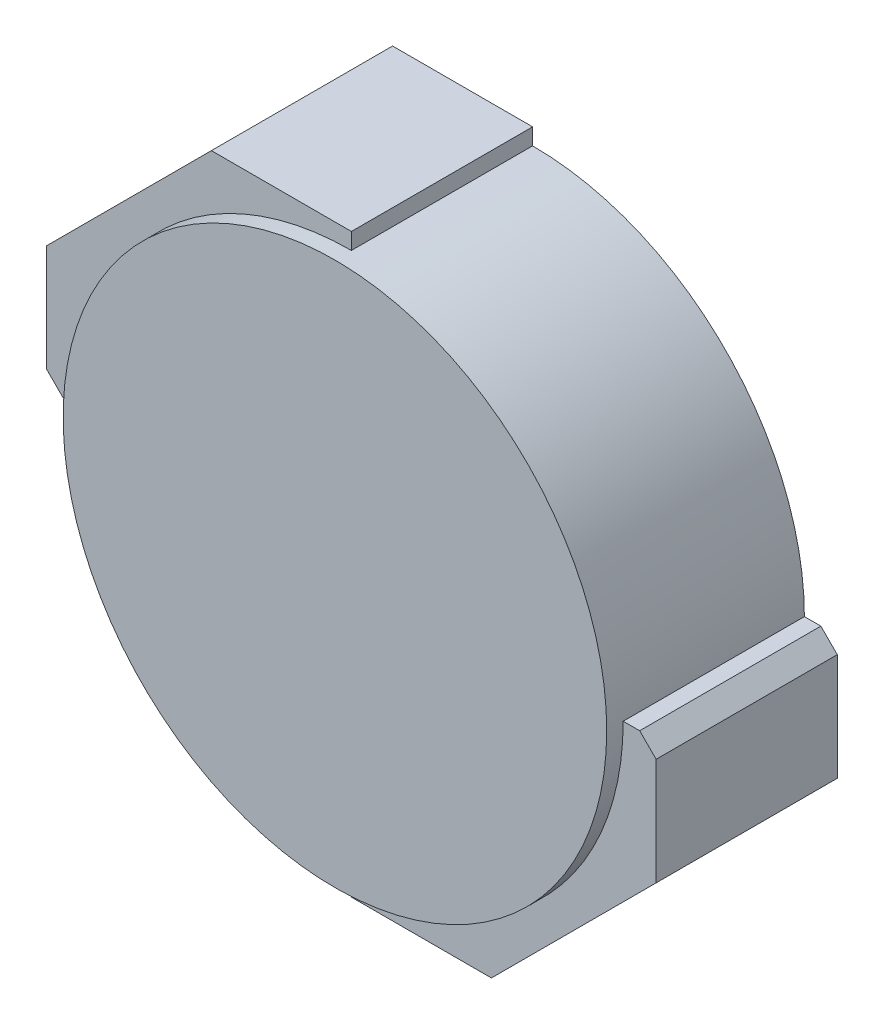
SolidWorks part; units mm, degrees
ref_plane "Front Plane" through (0, 0, 0) normal (0, 0, 1) x (1, 0, 0)
ref_plane "Top Plane" through (0, 0, 0) normal (0, 1, 0) x (1, 0, 0)
ref_plane "Right Plane" through (0, 0, 0) normal (1, 0, 0) x (0, 0, -1)
sketch "Sketch1" plane through (0, 0, 0) normal (0, 0, 1) x (1, 0, 0)
  circle A0 centre (0, 0) radius 1.65
extrude "Boss-Extrude1" add sketch "Sketch1" along normal blind 1.2
sketch "Sketch2" plane through (0, 0, 0) normal (0, 0, 1) x (1, 0, 0)
  line L5 (-1.85, 1.75) -> (0, 1.75)
  line L6 (-1.85, 1.75) -> (-1.85, 0)
  line L7 (-1.85, 0) -> (0, 0)
  line L8 (0, 1.75) -> (0, 0)
  line L9 (1.85, 0) -> (0, 0)
  line L10 (1.85, 0) -> (1.85, -1.75)
  line L11 (1.85, -1.75) -> (0, -1.75)
  line L12 (0, 0) -> (0, -1.75)
extrude "Boss-Extrude2" add sketch "Sketch2" along normal blind 1.1 contours L8 L5 L6 L7 | L9 L12 L11 L10
chamfer "Chamfer1" distance 0.1 angle 45 2 edges at (1.85, 0, 0.55) (-1.85, 0, 0.55)
chamfer "Chamfer2" distance 1 angle 45 2 edges at (1.85, -1.75, 0.55) (-1.85, 1.75, 0.55)
